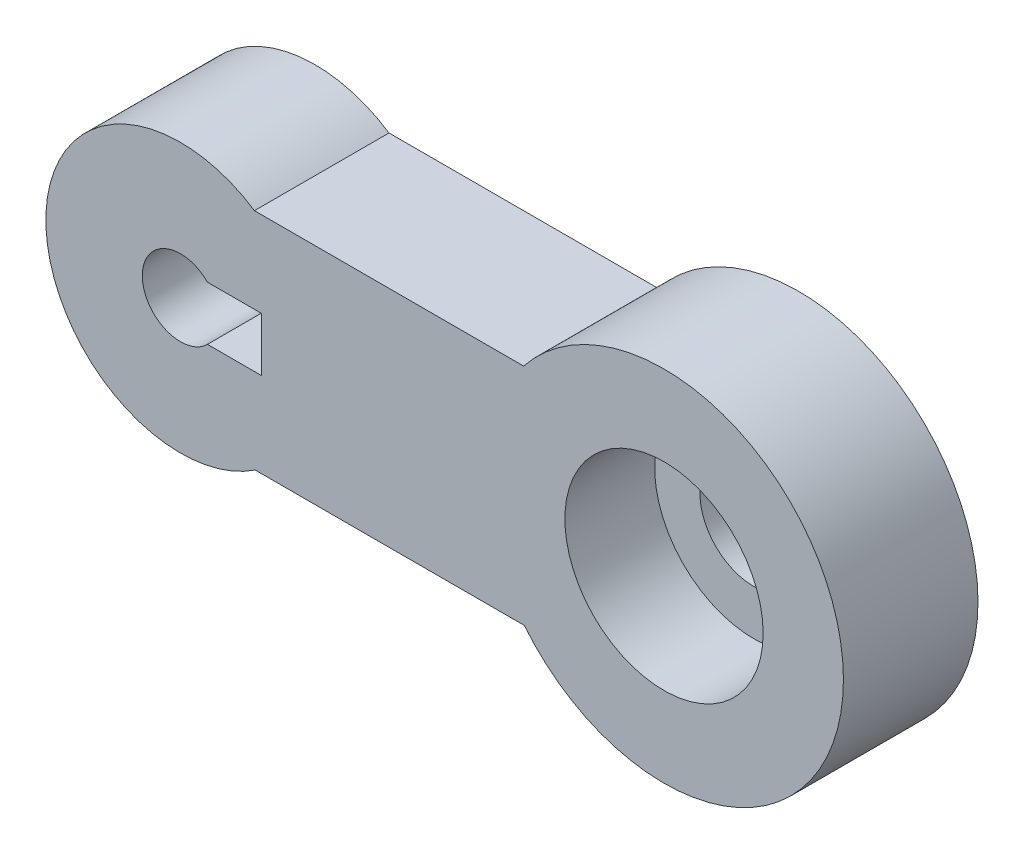
SolidWorks part; units mm, degrees
ref_plane "Front Plane" through (0, 0, 0) normal (0, 0, 1) x (1, 0, 0)
ref_plane "Top Plane" through (0, 0, 0) normal (0, 1, 0) x (1, 0, 0)
ref_plane "Right Plane" through (0, 0, 0) normal (1, 0, 0) x (0, 0, -1)
sketch "Sketch1" plane through (0, 0, 0) normal (0, 0, 1) x (1, 0, 0)
  line L0 (-25.1854, -3.1574) -> (-17.4882, -3.0516) construction
  line L1 (-16.8658, -15.6292) -> (13.1342, -15.6292)
  line L3 (-16.9451, 9.3708) -> (13.0549, 9.3708)
  line L5 (-9.868, -3.1657) -> (44.1933, 0.1512) construction
  line L6 (-25.1969, 9.3708) -> (27.0524, -13.7987) construction
  arc A0 (13.1342, -15.6292) -> (13.0549, 9.3708) centre (28.7069, -3.0797) ccw
  arc A1 (-16.9451, 9.3708) -> (-16.8658, -15.6292) centre (-25.1969, -3.1555) ccw
  circle A2 centre (-25.1969, -3.1555) radius 4.25
  point P0 (1.5011, -2.4681)
  dimension "D3" = 40
  dimension "D4" = 30
  dimension "D6" = 8.5
  dimension "D1" = 70
  dimension "D2" = 22.1
  dimension "D5" = 0
  dimension "D7" = 30
  dimension "D8" = 30
extrude "Boss-Extrude1" add sketch "Sketch1" along normal blind 15
sketch "Sketch2" plane through (0, 0, 15) normal (0, 0, 1) x (1, 0, 0)
  circle A0 centre (28.7069, -3.0797) radius 11.05
  arc A1 (13.1342, -15.6292) -> (13.0549, 9.3708) centre (28.7069, -3.0797) ccw construction
  dimension "D2" = 22.1
  dimension "D1" = 0
extrude "Cut-Extrude1" cut sketch "Sketch2" against normal blind 10
sketch "Sketch3" plane through (0, 0, 5) normal (0, 0, 1) x (1, 0, 0)
  circle A0 centre (28.7069, -3.0797) radius 6
  circle A1 centre (28.7069, -3.0797) radius 11.05 construction
  dimension "D2" = 12
  dimension "D1" = 0
extrude "Cut-Extrude2" cut sketch "Sketch3" against normal blind 10
sketch "Sketch5" plane through (0, 0, 15) normal (0, 0, 1) x (1, 0, 0)
  line L1 (-16.1865, -0.1555) -> (-22.1865, -0.1555)
  line L2 (-16.1865, -0.1555) -> (-16.1865, -6.1555)
  line L3 (-16.1865, -6.1555) -> (-22.1865, -6.1555)
  arc A0 (-22.1865, -0.1555) -> (-22.1865, -6.1555) centre (-25.1969, -3.1555) ccw
  circle A1 centre (-25.1969, -3.1555) radius 4.25 construction
  dimension "D1" = 0
  dimension "D2" = 8.5
  dimension "D5" = 6
  dimension "D6" = 6
extrude "Cut-Extrude5" cut sketch "Sketch5" against normal blind 15
